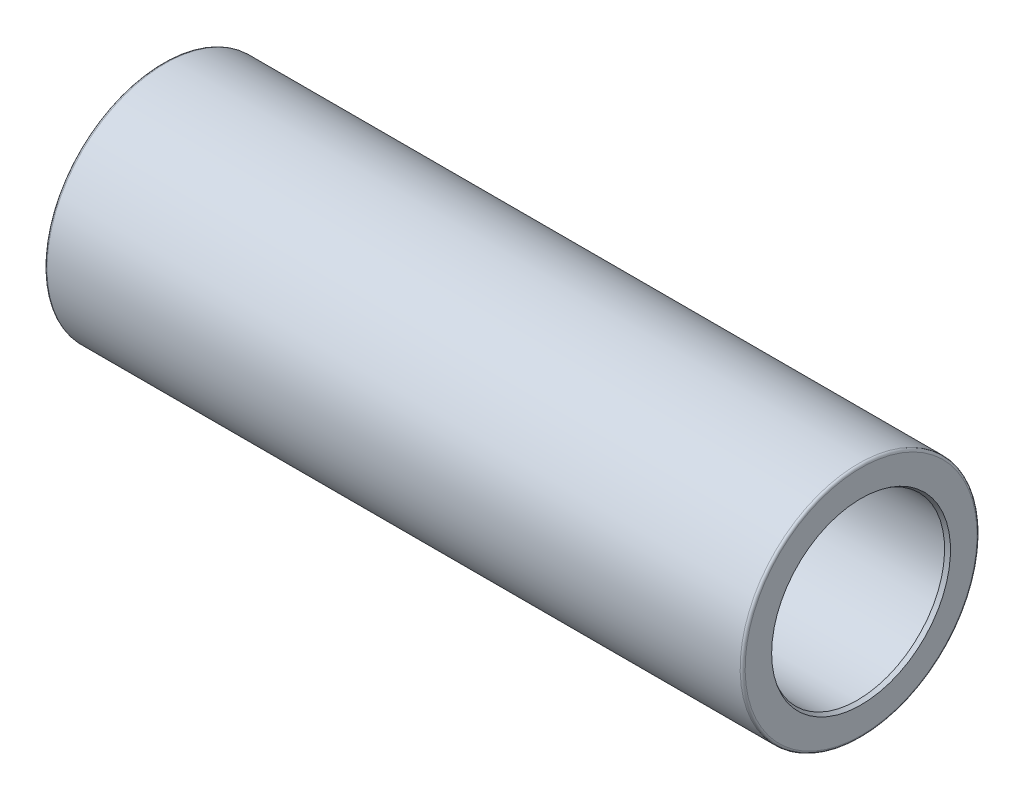
SolidWorks part; units mm, degrees
ref_plane "Plane1" through (0, 0, 0) normal (0, 0, 1) x (1, 0, 0)
ref_plane "Plane2" through (0, 0, 0) normal (0, 1, 0) x (1, 0, 0)
ref_plane "Plane3" through (0, 0, 0) normal (1, 0, 0) x (0, 0, -1)
sketch "Sketch1" plane through (0, 0, 0) normal (0, 0, 1) x (1, 0, 0)
  line L0 (-140, 0) -> (140, 0) construction
  line L1 (0, 93.3) -> (0, -101.2) construction
  line L2 (-140, 35) -> (-140, 46.5)
  line L3 (-139, 47.5) -> (139, 47.5)
  line L5 (-140, 35) -> (-73.4626, 35)
  line L6 (-73.4626, 35) -> (-71.5, 36)
  line L7 (-71.5, 36) -> (-69.5, 36)
  line L8 (-69.5, 36) -> (-69.5, 34)
  line L9 (-69.5, 34) -> (-60.1763, 34)
  line L10 (69.5, 36) -> (69.5, 34)
  line L11 (71.5, 36) -> (69.5, 36)
  line L12 (73.4626, 35) -> (71.5, 36)
  line L13 (140, 35) -> (73.4626, 35)
  line L15 (140, 35) -> (140, 46.5)
  line L16 (-59.8343, 34.0603) -> (-50.5495, 37.4397)
  line L17 (-50.2075, 37.5) -> (50.2075, 37.5)
  line L18 (59.8343, 34.0603) -> (50.5495, 37.4397)
  line L19 (60.1763, 34) -> (69.5, 34)
  arc A0 (-50.2075, 37.5) -> (-50.5495, 37.4397) centre (-50.2075, 36.5) ccw
  arc A1 (-60.1763, 34) -> (-59.8343, 34.0603) centre (-60.1763, 35) ccw
  arc A2 (50.2075, 37.5) -> (50.5495, 37.4397) centre (50.2075, 36.5) cw
  arc A3 (60.1763, 34) -> (59.8343, 34.0603) centre (60.1763, 35) cw
  arc A4 (-139, 47.5) -> (-140, 46.5) centre (-139, 46.5) ccw
  arc A5 (139, 47.5) -> (140, 46.5) centre (139, 46.5) cw
  point P23 (0, 47.5)
  point P26 (0, 37.5)
  point P28 (-50.3838, 37.5)
  point P31 (-60, 34)
  point P34 (50.3838, 37.5)
  point P37 (60, 34)
  point P40 (-140, 47.5)
  point P43 (140, 47.5)
  dimension "D14" = 1
  dimension "D15" = 1
  dimension "D1" = 280
  dimension "D2" = 95
  dimension "D4" = 27
  dimension "D5" = 70.5
  dimension "D6" = 70
  dimension "D7" = 75
  dimension "D9" = 2
  dimension "D10" = 72
  dimension "D11" = 68
  dimension "D12" = 20
  dimension "D13" = 80
revolve "Base-Revolve" add sketch "Sketch1" angle 360 about L0
sketch "Sketch5" plane through (0, 0, 0) normal (0, 0, 1) x (1, 0, 0)
  line L0 (0, 0) -> (140, 0) construction
  line L1 (140, -46.5) -> (140, 46.5) construction
  line L2 (140, 35.866) -> (138.5, 35)
  line L3 (140, 35) -> (73.4626, 35) construction
  line L4 (0, 0) -> (0, 47.5) construction
  line L5 (140, 35) -> (138.5, 35)
  line L6 (140, 35) -> (140, 35.866)
  line L7 (139, 47.5) -> (-139, 47.5) construction
  line L8 (-140, 35) -> (-140, 35.866)
  line L9 (-140, 35) -> (-138.5, 35)
  line L10 (-140, 35.866) -> (-138.5, 35)
  dimension "D1" = 30
  dimension "D2" = 1.5
revolve "2.5 x 30 gr reifning" cut sketch "Sketch5" angle 360 about L0
sketch "Sketch4" plane through (0, 0, 0) normal (1, 0, 0) x (0, 0, -1)
  line L1 (0, 0) -> (47.5, 0) construction
  line L2 (47.5, 0) -> (47.5, 10)
  line L3 (47.5, 10) -> (45.5, 10)
  line L4 (45.5, 10) -> (42.1352, 4.4)
  line L5 (42.1352, 4.4) -> (17.5, 4.4)
  line L6 (17.5, 4.4) -> (17.5, 0)
  line L7 (47.5, 0) -> (17.5, 0)
  line L8 (0, 0) -> (0, 47.5) construction
  circle A1 centre (0, 0) radius 47.5 construction
  circle A2 centre (0, 0) radius 47.5 construction
  dimension "D1" = 90
  dimension "D2" = 20
  dimension "D3" = 8.8
  dimension "D4" = 59
  dimension "D5" = 2
  dimension "D6" = 30
revolve "Udboring smørenippel" [suppressed] cut sketch "Sketch4" angle 360 about L1
cosmetic thread "Cosmetic Thread1" [suppressed] parameters "D2"=9.728
